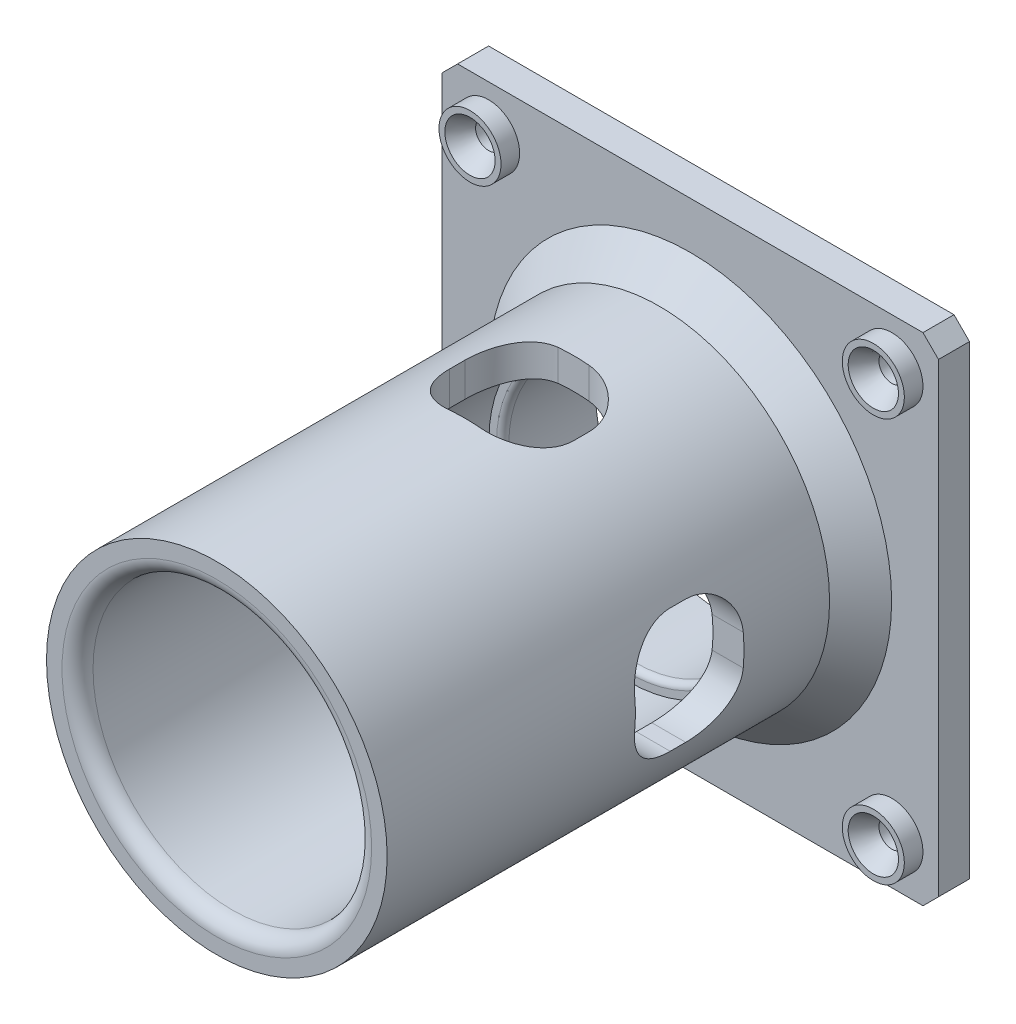
SolidWorks part; units mm, degrees
ref_plane "Front Plane" through (0, 0, 0) normal (0, 0, 1) x (1, 0, 0)
ref_plane "Top Plane" through (0, 0, 0) normal (0, 1, 0) x (1, 0, 0)
ref_plane "Right Plane" through (0, 0, 0) normal (1, 0, 0) x (0, 0, -1)
sketch "Sketch1" plane through (0, 0, 0) normal (0, 0, 1) x (1, 0, 0)
  circle A0 centre (0, 0) radius 22.45
  circle A1 centre (0, 0) radius 27.45
  point P0 (0, 0)
  dimension "D1" = 44.9
  dimension "D2" = 5
extrude "Boss-Extrude1" add sketch "Sketch1" along normal blind 76.3
sketch "Sketch2" plane through (0, 0, 0) normal (0, 0, -1) x (-1, 0, 0)
  line L1 (-40, 40) -> (40, 40)
  line L2 (-40, 40) -> (-40, -40)
  line L3 (-40, -40) -> (40, -40)
  line L4 (40, 40) -> (40, -40)
  line L5 (-40, 40) -> (40, -40) construction
  line L6 (-40, -40) -> (40, 40) construction
  point P0 (0, 0)
  dimension "D1" = 80
  dimension "D2" = 80
extrude "Boss-Extrude2" add sketch "Sketch2" along normal blind 5
sketch "Sketch3" plane through (0, 0, 0) normal (0, 0, 1) x (1, 0, 0)
  line L0 (-40, -40) -> (-40, 40) construction
  line L1 (-40, 40) -> (40, 40) construction
  circle A0 centre (-32.5, 32.5) radius 5
  dimension "D1" = 10
  dimension "D2" = 7.5
  dimension "D3" = 7.5
extrude "Boss-Extrude3" add sketch "Sketch3" along normal blind 3
sketch "Sketch4" plane through (0, 0, 3) normal (0, 0, 1) x (1, 0, 0)
  circle A0 centre (-32.5, 32.5) radius 2.1
  circle A1 centre (32.5, 32.5) radius 2.1
  circle A2 centre (32.5, -32.5) radius 2.1
  circle A3 centre (-32.5, -32.5) radius 2.1
  dimension "D1" = 4.2
  dimension "D2" = 2
  dimension "D3" = 2
extrude "Cut-Extrude1" cut sketch "Sketch4" against normal through all
sketch "Sketch5" plane through (0, 0, 0) normal (0, 0, 1) x (1, 0, 0)
  circle A0 centre (-32.5, 32.5) radius 2.1 construction
sketch "Sketch6" plane through (0, 0, 3) normal (0, 0, 1) x (1, 0, 0)
  circle A0 centre (-32.5, 32.5) radius 4.05 construction
  dimension "D1" = 8.1
ref_plane "Plane1" through (-32.5, 0, 0) normal (-1, 0, 0) x (0, 0, 1)
sketch "Sketch7" plane through (-32.5, 0, 0) normal (-1, 0, 0) x (0, 0, 1)
  line L0 (3, 32.5) -> (0, 32.5)
  line L2 (3, 28.45) -> (3, 32.5)
  line L3 (3, 28.45) -> (3, 36.55) construction
  line L4 (0, 32.5) -> (0, 30.4)
  line L5 (0, 30.4) -> (3, 28.45)
revolve "Cut-Revolve1" cut sketch "Sketch7" angle 360 about L0
pattern_linear "LPattern1" count 2 spacing 65 along (1, 0, 0) count 2 spacing 65 along (0, -1, 0) of "Boss-Extrude3"
pattern_linear "LPattern2" count 2 spacing 65 along (1, 0, 0) count 2 spacing 65 along (0, -1, 0) of "Cut-Revolve1"
sketch "Sketch8" plane through (0, 0, 0) normal (0, 0, 1) x (1, 0, 0)
  circle A0 centre (0, 0) radius 20.25
  dimension "D1" = 40.5
extrude "Cut-Extrude2" cut sketch "Sketch8" against normal through all
sketch "Sketch10" plane through (0, 0, 0) normal (0, 0, 1) x (1, 0, 0)
  circle A0 centre (0, 0) radius 20.25
  circle A1 centre (0, 0) radius 22.45
  circle A2 centre (0, 0) radius 20.25 construction
  circle A3 centre (0, 0) radius 22.45 construction
extrude "Boss-Extrude4" add sketch "Sketch10" along normal blind 10
sketch "Sketch9" plane through (0, -40, 0) normal (0, -1, 0) x (1, 0, 0)
  line L0 (0, 76.3) -> (0, 36.3) construction
  line L1 (22.45, 76.3) -> (-22.45, 76.3) construction
  line L3 (-10, 36.3) -> (10, 36.3)
  line L4 (-10, 36.3) -> (-10, 18.8)
  line L5 (-10, 18.8) -> (10, 18.8)
  line L6 (10, 36.3) -> (10, 18.8)
  dimension "D1" = 40
  dimension "D2" = 20
  dimension "D3" = 17.5
extrude "Cut-Extrude3" cut sketch "Sketch9" against normal blind 40
fillet "Fillet1" radius 7.5 4 edges at (-10, -22.8318, 18.8) (10, -22.8318, 18.8) (10, -22.8318, 36.3) (-10, -22.8318, 36.3)
pattern_circular "CirPattern1" count 4 over 360 about axis through (0, 0, 0) along (0, 0, 1) of "Cut-Extrude3", "Fillet1"
fillet "Fillet2" radius 2.5 1 edges at (22.45, 0, 76.3)
chamfer "Chamfer1" distance 5 angle 45 1 edges at (27.45, 0, 0)
chamfer "Chamfer2" distance 2.5 angle 45 4 edges at (-40, 40, -2.5) (40, 40, -2.5) (-40, -40, -2.5) (40, -40, -2.5)
fillet "Fillet3" radius 1 1 edges at (20.25, 0, 10)
